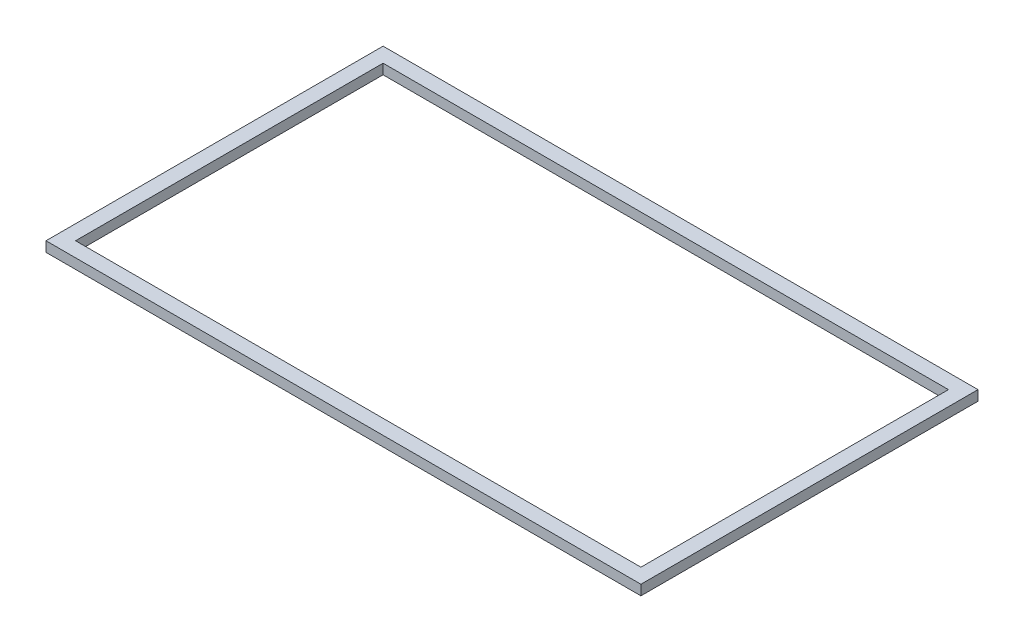
SolidWorks part; units mm, degrees
ref_plane "Ebene vorne" through (0, 0, 0) normal (0, 0, 1) x (1, 0, 0)
ref_plane "Ebene oben" through (0, 0, 0) normal (0, 1, 0) x (1, 0, 0)
ref_plane "Ebene rechts" through (0, 0, 0) normal (1, 0, 0) x (0, 0, -1)
sketch "Skizze2" plane through (0, 0, 0) normal (0, 1, 0) x (1, 0, 0)
  line L5 (-43.2, -24) -> (43.2, -24) construction
  line L6 (-43.2, -24) -> (-43.2, 24) construction
  line L11 (-43.2, 24) -> (43.2, 24) construction
  line L12 (43.2, -24) -> (43.2, 24) construction
  line L13 (-43.2, -24) -> (43.2, 24) construction
  line L14 (-43.2, 24) -> (43.2, -24) construction
  line L15 (-42.1, -22.9) -> (42.1, -22.9)
  line L16 (-42.1, -22.9) -> (-42.1, 22.9)
  line L17 (-42.1, 22.9) -> (42.1, 22.9)
  line L18 (42.1, -22.9) -> (42.1, 22.9)
  line L19 (-42.1, -22.9) -> (42.1, 22.9) construction
  line L20 (-42.1, 22.9) -> (42.1, -22.9) construction
  line L21 (-44.3, -25.1) -> (44.3, -25.1)
  line L22 (-44.3, -25.1) -> (-44.3, 25.1)
  line L23 (-44.3, 25.1) -> (44.3, 25.1)
  line L24 (44.3, -25.1) -> (44.3, 25.1)
  line L25 (-44.3, -25.1) -> (44.3, 25.1) construction
  line L26 (-44.3, 25.1) -> (44.3, -25.1) construction
  point P0 (0, 0)
  point P5 (0, 0)
  point P10 (0, 0)
  dimension "D1" = 48
  dimension "D2" = 86.4
  dimension "D3" = 1.1
  dimension "D4" = 1.1
  dimension "D5" = 1.1
  dimension "D6" = 1.1
extrude "Aufsatz-Linear austragen1" add sketch "Skizze2" along normal blind 1.5
